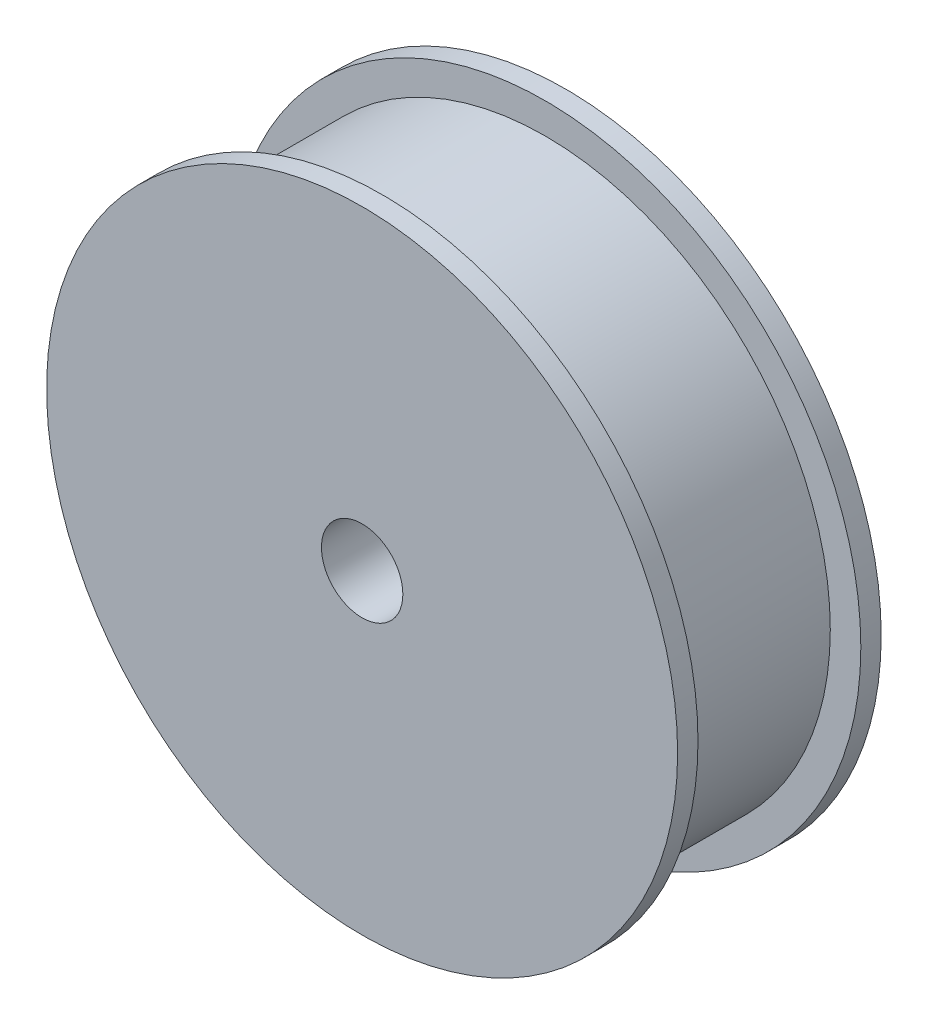
SolidWorks part; units mm, degrees
ref_plane "Front Plane" through (0, 0, 0) normal (1, 0, 0) x (0, 1, 0)
ref_plane "Top Plane" through (0, 0, 0) normal (0, 0, 1) x (0, 1, 0)
ref_plane "Right Plane" through (0, 0, 0) normal (0, 1, 0) x (-1, 0, 0)
sketch "Sketch1" plane through (0, 0, 0) normal (0, 0, 1) x (0, 1, 0)
  circle A0 centre (0, 0) radius 31
  dimension "D1" = 62
extrude "Boss-Extrude1" add sketch "Sketch1" along normal blind 20
ref_plane "Plane1" through (0, 0, 2) normal (0, 0, 1) x (0, 1, 0)
sketch "Sketch2" plane through (0, 0, 2) normal (0, 0, 1) x (0, 1, 0)
  circle A0 centre (0, 0) radius 28
  circle A1 centre (0, 0) radius 31
  dimension "D1" = 56
extrude "Cut-Extrude1" cut sketch "Sketch2" along normal blind 16
sketch "Sketch3" plane through (0, 0, 20) normal (0, 0, 1) x (1, 0, 0)
  circle A0 centre (0, 0) radius 4
  dimension "D1" = 8
extrude "Cut-Extrude2" cut sketch "Sketch3" against normal through all
